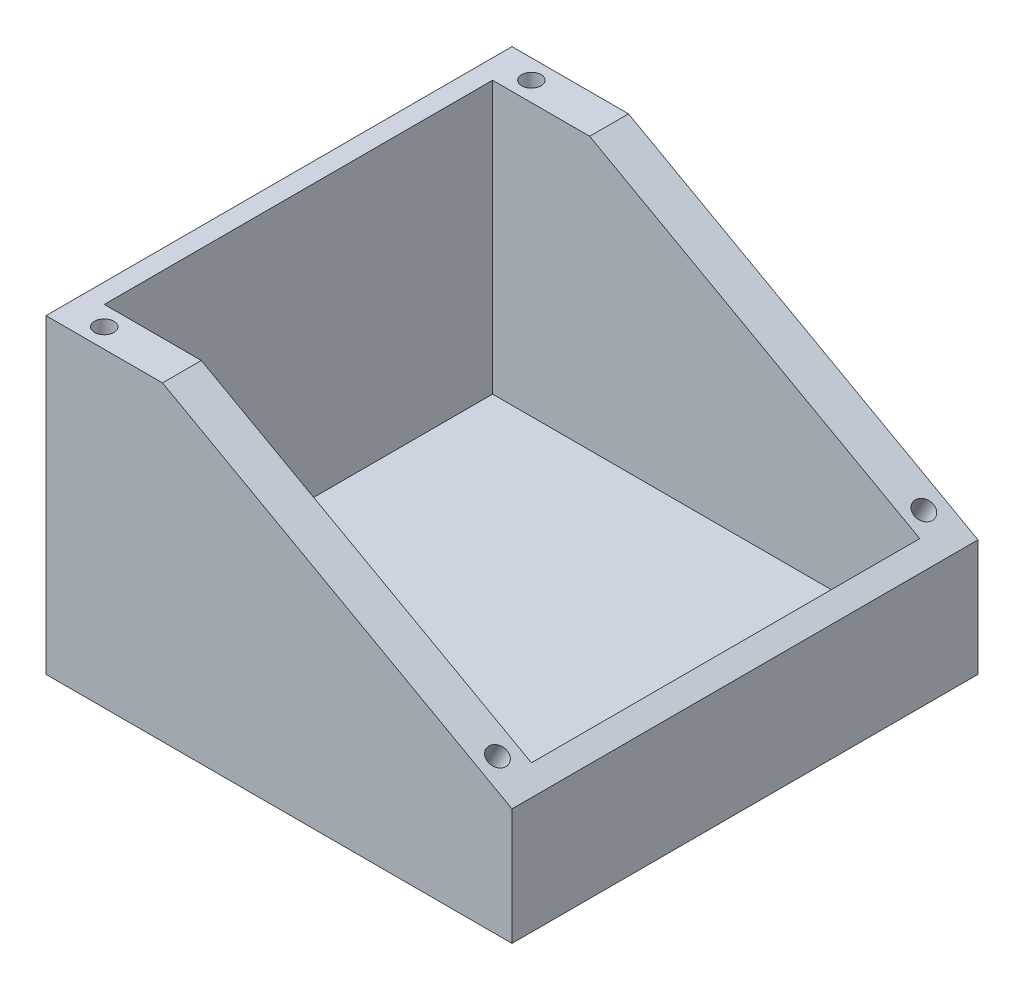
SolidWorks part; units mm, degrees
ref_plane "Front Plane" through (0, 0, 0) normal (0, 0, 1) x (1, 0, 0)
ref_plane "Top Plane" through (0, 0, 0) normal (0, 1, 0) x (1, 0, 0)
ref_plane "Right Plane" through (0, 0, 0) normal (1, 0, 0) x (0, 0, -1)
sketch "Sketch1" plane through (0, 0, 0) normal (0, 0, 1) x (1, 0, 0)
  line L0 (0, 0) -> (0, 101.6)
  line L1 (0, 101.6) -> (152.4, 101.6)
  line L2 (152.4, 101.6) -> (152.4, 0)
  line L3 (152.4, 0) -> (0, 0)
  dimension "D1" = 101.6
  dimension "D2" = 152.4
extrude "Boss-Extrude1" add sketch "Sketch1" along normal blind 152.4
sketch "Sketch6" plane through (0, 0, 152.4) normal (0, 0, 1) x (1, 0, 0)
  line L0 (38.1, 101.6) -> (152.4, 101.6)
  line L1 (152.4, 101.6) -> (0, 101.6) construction
  line L2 (152.4, 101.6) -> (152.4, 38.1)
  line L3 (152.4, 0) -> (152.4, 101.6) construction
  line L4 (152.4, 38.1) -> (38.1, 101.6)
  line L5 (104.4367, 101.6) -> (104.5902, 101.6)
  line M5 (152.4, 0) -> (152.4, 101.6)
  line M6 (152.4, 101.6) -> (0, 101.6)
  dimension "D1" = 63.5
  dimension "D2" = 114.3
extrude "Cut-Extrude2" cut sketch "Sketch6" against normal blind 152.4 contours L4 L0 M5 M6
sketch "Sketch7" plane through (0, 101.6, 0) normal (0, 1, 0) x (1, 0, 0)
  line L0 (6.35, -12.7) -> (6.35, -139.7)
  line L1 (6.35, -139.7) -> (146.05, -139.7)
  line L2 (146.05, -139.7) -> (146.05, -12.7)
  line L3 (146.05, -12.7) -> (6.35, -12.7)
  line L4 (38.1, 0) -> (0, 0) construction
  line L5 (0, -152.4) -> (0, 0) construction
  line L6 (152.4, -152.4) -> (38.1, -152.4) construction
  line L7 (152.4, 0) -> (152.4, -152.4) construction
  dimension "D1" = 12.7
  dimension "D2" = 6.35
  dimension "D3" = 12.7
  dimension "D4" = 6.35
extrude "Cut-Extrude3" cut sketch "Sketch7" against normal blind 88.9
sketch "Sketch8" plane through (0, 101.6, 0) normal (0, 1, 0) x (1, 0, 0)
  line L0 (38.1, -152.4) -> (0, -152.4) construction
  line L1 (0, -152.4) -> (0, 0) construction
  line L2 (38.1, 0) -> (0, 0) construction
  circle A0 centre (12.7, -146.05) radius 3.175
  circle A1 centre (12.7, -6.35) radius 3.175
  dimension "D1" = 6.35
  dimension "D2" = 6.35
  dimension "D4" = 12.7
  dimension "D3" = 6.35
  dimension "D5" = 6.35
  dimension "D6" = 12.7
extrude "Cut-Extrude4" cut sketch "Sketch8" against normal blind 12.7
sketch "Sketch9" plane through (52.1179, 93.8123, 0) normal (0.4856, 0.8742, 0) x (0.8742, -0.4856, 0)
  line L0 (114.7186, -152.4) -> (-16.0359, -152.4) construction
  line L1 (114.7186, 0) -> (-16.0359, 0) construction
  line L2 (114.7186, 0) -> (114.7186, -152.4) construction
  circle A0 centre (102.0186, -146.05) radius 3.175
  circle A1 centre (102.0186, -6.604) radius 3.175
  dimension "D1" = 6.35
  dimension "D2" = 6.35
  dimension "D3" = 6.35
  dimension "D4" = 6.604
  dimension "D5" = 12.7
  dimension "D6" = 12.7
extrude "Cut-Extrude5" cut sketch "Sketch9" against normal blind 12.7
